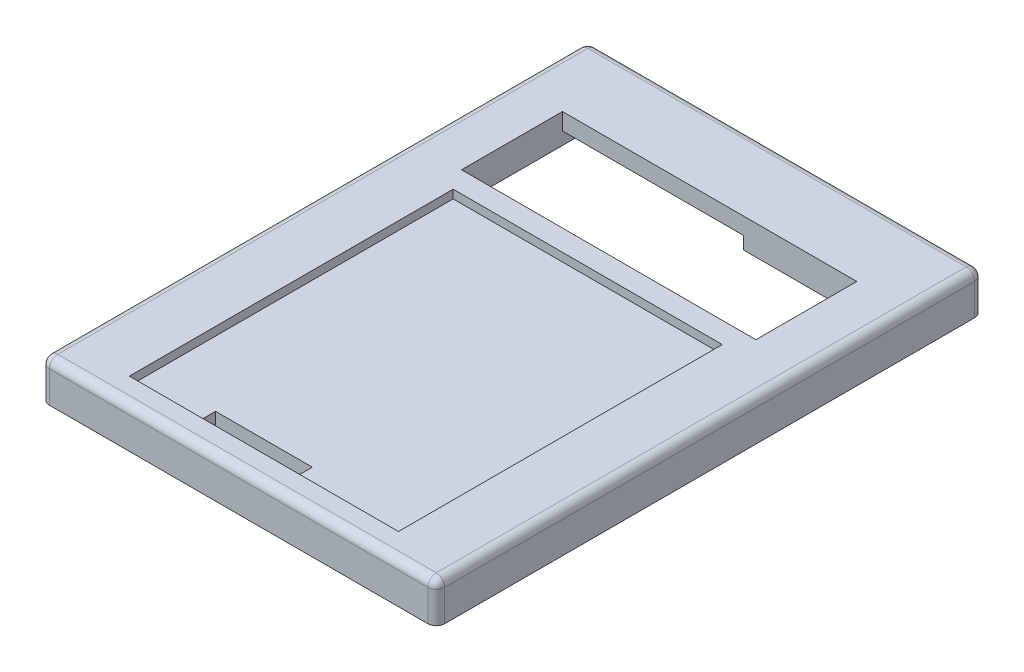
SolidWorks part; units mm, degrees
ref_plane "Front Plane" through (0, 0, 0) normal (0, 0, 1) x (1, 0, 0)
ref_plane "Top Plane" through (0, 0, 0) normal (0, 1, 0) x (1, 0, 0)
ref_plane "Right Plane" through (0, 0, 0) normal (1, 0, 0) x (0, 0, -1)
ref_plane "Plane1" through (0, 7, 0) normal (0, 1, 0) x (1, 0, 0)
sketch "Sketch1" plane through (0, 7, 0) normal (0, 1, 0) x (1, 0, 0)
  line L0 (0, 130) -> (0, 0)
  line L1 (0, 0) -> (94, 0)
  line L2 (94, 0) -> (94, 130)
  line L3 (94, 130) -> (0, 130)
extrude "Boss-Extrude1" add sketch "Sketch1" against normal blind 9.5
sketch "Sketch2" plane through (0, -2.5, 0) normal (0, -1, 0) x (1, 0, 0)
  line L0 (1.75, -128.25) -> (92.25, -128.25)
  line L1 (92.25, -128.25) -> (92.25, -1.75)
  line L2 (92.25, -1.75) -> (1.75, -1.75)
  line L3 (1.75, -1.75) -> (1.75, -128.25)
extrude "Cut-Extrude1" cut sketch "Sketch2" against normal blind 2.5
sketch "Sketch3" plane through (0, 0, 0) normal (0, -1, 0) x (1, 0, 0)
  line L0 (82, -88) -> (12, -88)
  line L1 (12, -88) -> (12, -112)
  line L2 (12, -112) -> (82, -112)
  line L3 (82, -112) -> (82, -88)
  line L7 (94, -130) -> (0, -130) construction
  point P4 (47, -112)
  point P7 (47, -130)
  dimension "D1" = 70
  dimension "D2" = 24
extrude "Cut-Extrude2" cut sketch "Sketch3" against normal through all
sketch "Sketch4" plane through (0, 7, 0) normal (0, 1, 0) x (-1, 0, 0)
  line L0 (-79, -83) -> (-15, -83)
  line L1 (-15, -83) -> (-15, -6)
  line L2 (-15, -6) -> (-79, -6)
  line L3 (-79, -6) -> (-79, -83)
  line L4 (-94, -130) -> (0, -130) construction
  point P4 (-47, -83)
  point P7 (-47, -130)
  dimension "D1" = 64
  dimension "D2" = 77
extrude "Cut-Extrude3" cut sketch "Sketch4" against normal blind 2
sketch "Sketch5" plane through (0, 5, 0) normal (0, 1, 0) x (-1, 0, 0)
  line L0 (-30.5, -7.5) -> (-53.5, -7.5)
  line L1 (-53.5, -7.5) -> (-53.5, -11)
  line L2 (-53.5, -11) -> (-30.5, -11)
  line L3 (-30.5, -11) -> (-30.5, -7.5)
  line L4 (-15, -83) -> (-15, -6) construction
  dimension "D1" = 23
  dimension "D2" = 3.5
  dimension "D3" = 15.5
extrude "Cut-Extrude4" cut sketch "Sketch5" against normal through all
sketch "Sketch6" plane through (0, 0, 0) normal (0, -1, 0) x (1, 0, 0)
  line L0 (82, -109) -> (88, -109)
  line L1 (88, -109) -> (88, -91)
  line L2 (88, -91) -> (82, -91)
  line L3 (82, -91) -> (82, -109)
  line L4 (82, -112) -> (82, -88) construction
extrude "Cut-Extrude5" cut sketch "Sketch6" against normal blind 3.5
sketch "Sketch7" plane through (0, 0, 0) normal (0, -1, 0) x (1, 0, 0)
  line L0 (12, -112) -> (12, -119.5)
  line L1 (12, -119.5) -> (55, -119.5)
  line L2 (55, -119.5) -> (55, -112)
  line L3 (55, -112) -> (12, -112)
extrude "Cut-Extrude6" cut sketch "Sketch7" against normal blind 3
fillet "Fillet1" radius 2 8 edges at (0, 2.25, 0) (0, 2.25, -130) (0, 7, -65) (94, 2.25, 0) (47, 7, 0) (47, 7, -130) (94, 7, -65) (94, 2.25, -130)
